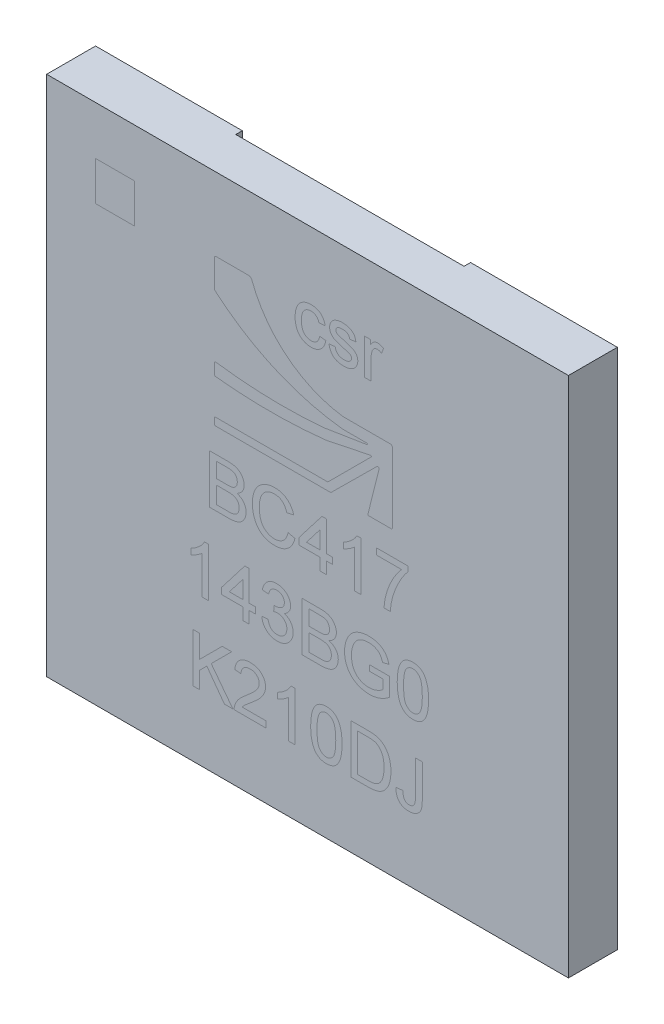
SolidWorks part; units mm, degrees
ref_plane "Спереди" through (0, 0, 0) normal (0, 0, 1) x (1, 0, 0)
ref_plane "Сверху" through (0, 0, 0) normal (0, 1, 0) x (1, 0, 0)
ref_plane "Справа" through (0, 0, 0) normal (1, 0, 0) x (0, 0, -1)
sketch "Эскиз1" plane through (0, 0, 0) normal (0, 0, 1) x (1, 0, 0)
  line L1 (4, 4) -> (-4, 4)
  line L2 (4, 4) -> (4, -4)
  line L3 (4, -4) -> (-4, -4)
  line L4 (-4, 4) -> (-4, -4)
  line L5 (4, 4) -> (-4, -4) construction
  line L6 (4, -4) -> (-4, 4) construction
  point P0 (0, 0)
  dimension "D1" = 8
  dimension "D2" = 8
extrude "Бобышка-Вытянуть1" add sketch "Эскиз1" along normal blind 0.75
sketch "Эскиз2" plane through (0, 0, 0) normal (0, 0, -1) x (-1, 0, 0)
  line L0 (0, -4) -> (0, 4) construction
  line L1 (4, -4) -> (-4, -4) construction
  line L2 (-4, 4) -> (4, 4) construction
  line L3 (4, 0) -> (-4, 0) construction
  line L4 (4, 4) -> (4, -4) construction
  line L5 (-4, -4) -> (-4, 4) construction
  line L6 (4, 4) -> (3.5986, 4) construction
  line L7 (3.5986, 4) -> (3.5986, 3.68) construction
  line L8 (3.5986, -4) -> (3.5986, -3.68) construction
  line L9 (4, -4) -> (3.5986, -4) construction
  line L10 (-4, -4) -> (-3.5986, -4) construction
  line L11 (-3.5986, -3.11) -> (-3.5986, -3.705) construction
  line L12 (-3.5986, 4) -> (-3.5986, 3.68) construction
  line L13 (-4, 4) -> (-3.5986, 4) construction
  circle A0 centre (3.5986, 3.68) radius 0.154
  circle A1 centre (3.5986, 3.11) radius 0.154
  circle A2 centre (3.5986, 2.54) radius 0.154
  circle A3 centre (3.5986, 1.97) radius 0.154
  circle A4 centre (3.5986, 1.4) radius 0.154
  circle A5 centre (3.5986, 0.83) radius 0.154
  circle A6 centre (3.5986, 0.26) radius 0.154
  circle A14 centre (3.1486, 3.11) radius 0.154
  circle A15 centre (3.1486, 2.54) radius 0.154
  circle A16 centre (3.1486, 1.97) radius 0.154
  circle A17 centre (3.1486, 1.4) radius 0.154
  circle A18 centre (3.1486, 0.83) radius 0.154
  circle A19 centre (3.1486, 0.26) radius 0.154
  circle A27 centre (2.6986, 3.11) radius 0.154
  circle A28 centre (2.6986, 2.54) radius 0.154
  circle A29 centre (2.6986, 1.97) radius 0.154
  circle A30 centre (2.6986, 1.4) radius 0.154
  circle A31 centre (2.6986, 0.83) radius 0.154
  circle A32 centre (2.6986, 0.26) radius 0.154
  circle A40 centre (2.2486, 3.11) radius 0.154
  circle A41 centre (2.2486, 2.54) radius 0.154
  circle A42 centre (2.2486, 1.97) radius 0.154
  circle A43 centre (2.2486, 1.4) radius 0.154
  circle A44 centre (2.2486, 0.83) radius 0.154
  circle A45 centre (2.2486, 0.26) radius 0.154
  circle A53 centre (3.1486, 3.68) radius 0.154
  circle A54 centre (2.6986, 3.68) radius 0.154
  circle A55 centre (2.2486, 3.68) radius 0.154
  circle A112 centre (3.5986, -0.31) radius 0.154 [skipped]
  circle A113 centre (3.5986, -0.88) radius 0.154 [skipped]
  circle A114 centre (3.5986, -1.45) radius 0.154 [skipped]
  circle A115 centre (3.5986, -2.02) radius 0.154 [skipped]
  circle A116 centre (3.5986, -2.59) radius 0.154 [skipped]
  circle A117 centre (3.5986, -3.16) radius 0.154 [skipped]
  circle A118 centre (3.5986, -3.73) radius 0.154 [skipped]
  circle A119 centre (3.1486, -0.31) radius 0.154 [skipped]
  circle A120 centre (3.1486, -0.88) radius 0.154 [skipped]
  circle A121 centre (3.1486, -1.45) radius 0.154 [skipped]
  circle A122 centre (3.1486, -2.02) radius 0.154 [skipped]
  circle A123 centre (3.1486, -2.59) radius 0.154 [skipped]
  circle A124 centre (3.1486, -3.16) radius 0.154 [skipped]
  circle A125 centre (3.1486, -3.73) radius 0.154 [skipped]
  circle A126 centre (2.6986, -0.31) radius 0.154 [skipped]
  circle A127 centre (2.6986, -0.88) radius 0.154 [skipped]
  circle A128 centre (2.6986, -1.45) radius 0.154 [skipped]
  circle A129 centre (2.6986, -2.02) radius 0.154 [skipped]
  circle A130 centre (2.6986, -2.59) radius 0.154 [skipped]
  circle A131 centre (2.6986, -3.16) radius 0.154 [skipped]
  circle A132 centre (2.6986, -3.73) radius 0.154 [skipped]
  circle A133 centre (2.2486, -0.31) radius 0.154 [skipped]
  circle A134 centre (2.2486, -0.88) radius 0.154 [skipped]
  circle A135 centre (2.2486, -1.45) radius 0.154 [skipped]
  circle A136 centre (2.2486, -2.02) radius 0.154 [skipped]
  circle A137 centre (2.2486, -2.59) radius 0.154 [skipped]
  circle A138 centre (2.2486, -3.16) radius 0.154 [skipped]
  circle A139 centre (2.2486, -3.73) radius 0.154 [skipped]
  circle A140 centre (2.2486, -3.68) radius 0.154
  circle A141 centre (2.6986, -3.68) radius 0.154
  circle A142 centre (3.1486, -3.68) radius 0.154
  circle A143 centre (2.2486, -0.26) radius 0.154
  circle A144 centre (2.2486, -0.83) radius 0.154
  circle A145 centre (2.2486, -1.4) radius 0.154
  circle A146 centre (2.2486, -1.97) radius 0.154
  circle A147 centre (2.2486, -2.54) radius 0.154
  circle A148 centre (2.2486, -3.11) radius 0.154
  circle A149 centre (2.6986, -0.26) radius 0.154
  circle A150 centre (2.6986, -0.83) radius 0.154
  circle A151 centre (2.6986, -1.4) radius 0.154
  circle A152 centre (2.6986, -1.97) radius 0.154
  circle A153 centre (2.6986, -2.54) radius 0.154
  circle A154 centre (2.6986, -3.11) radius 0.154
  circle A155 centre (3.1486, -0.26) radius 0.154
  circle A156 centre (3.1486, -0.83) radius 0.154
  circle A157 centre (3.1486, -1.4) radius 0.154
  circle A158 centre (3.1486, -1.97) radius 0.154
  circle A159 centre (3.1486, -2.54) radius 0.154
  circle A160 centre (3.1486, -3.11) radius 0.154
  circle A161 centre (3.5986, -0.26) radius 0.154
  circle A162 centre (3.5986, -0.83) radius 0.154
  circle A163 centre (3.5986, -1.4) radius 0.154
  circle A164 centre (3.5986, -1.97) radius 0.154
  circle A165 centre (3.5986, -2.54) radius 0.154
  circle A166 centre (3.5986, -3.11) radius 0.154
  circle A169 centre (-3.5986, -3.11) radius 0.154
  circle A170 centre (-3.5986, -2.54) radius 0.154
  circle A171 centre (-3.5986, -1.97) radius 0.154
  circle A172 centre (-3.5986, -1.4) radius 0.154
  circle A173 centre (-3.5986, -0.83) radius 0.154
  circle A174 centre (-3.5986, -0.26) radius 0.154
  circle A175 centre (-3.1486, -3.11) radius 0.154
  circle A176 centre (-3.1486, -2.54) radius 0.154
  circle A177 centre (-3.1486, -1.97) radius 0.154
  circle A178 centre (-3.1486, -1.4) radius 0.154
  circle A179 centre (-3.1486, -0.83) radius 0.154
  circle A180 centre (-3.1486, -0.26) radius 0.154
  circle A181 centre (-2.6986, -3.11) radius 0.154
  circle A182 centre (-2.6986, -2.54) radius 0.154
  circle A183 centre (-2.6986, -1.97) radius 0.154
  circle A184 centre (-2.6986, -1.4) radius 0.154
  circle A185 centre (-2.6986, -0.83) radius 0.154
  circle A186 centre (-2.6986, -0.26) radius 0.154
  circle A187 centre (-2.2486, -3.11) radius 0.154
  circle A188 centre (-2.2486, -2.54) radius 0.154
  circle A189 centre (-2.2486, -1.97) radius 0.154
  circle A190 centre (-2.2486, -1.4) radius 0.154
  circle A191 centre (-2.2486, -0.83) radius 0.154
  circle A192 centre (-2.2486, -0.26) radius 0.154
  circle A193 centre (-3.1486, -3.68) radius 0.154
  circle A194 centre (-2.6986, -3.68) radius 0.154
  circle A195 centre (-2.2486, -3.68) radius 0.154
  circle A196 centre (-2.2486, 3.68) radius 0.154
  circle A197 centre (-2.6986, 3.68) radius 0.154
  circle A198 centre (-3.1486, 3.68) radius 0.154
  circle A199 centre (-2.2486, 0.26) radius 0.154
  circle A200 centre (-2.2486, 0.83) radius 0.154
  circle A201 centre (-2.2486, 1.4) radius 0.154
  circle A202 centre (-2.2486, 1.97) radius 0.154
  circle A203 centre (-2.2486, 2.54) radius 0.154
  circle A204 centre (-2.2486, 3.11) radius 0.154
  circle A205 centre (-2.6986, 0.26) radius 0.154
  circle A206 centre (-2.6986, 0.83) radius 0.154
  circle A207 centre (-2.6986, 1.4) radius 0.154
  circle A208 centre (-2.6986, 1.97) radius 0.154
  circle A209 centre (-2.6986, 2.54) radius 0.154
  circle A210 centre (-2.6986, 3.11) radius 0.154
  circle A211 centre (-3.1486, 0.26) radius 0.154
  circle A212 centre (-3.1486, 0.83) radius 0.154
  circle A213 centre (-3.1486, 1.4) radius 0.154
  circle A214 centre (-3.1486, 1.97) radius 0.154
  circle A215 centre (-3.1486, 2.54) radius 0.154
  circle A216 centre (-3.1486, 3.11) radius 0.154
  circle A217 centre (-3.5986, 0.26) radius 0.154
  circle A218 centre (-3.5986, 0.83) radius 0.154
  circle A219 centre (-3.5986, 1.4) radius 0.154
  circle A220 centre (-3.5986, 1.97) radius 0.154
  circle A221 centre (-3.5986, 2.54) radius 0.154
  circle A222 centre (-3.5986, 3.11) radius 0.154
  circle A223 centre (-3.5986, 3.68) radius 0.154
  circle A224 centre (-3.5986, -3.705) radius 0.154
  dimension "D1" = 14
  dimension "D3" = 0.308
  dimension "D4" = 0.32
  dimension "D2" = 4
extrude "Бобышка-Вытянуть2" add sketch "Эскиз2" along normal blind 0.1
sketch "Эскиз3" plane through (0, 0, 0) normal (0, 0, -1) x (-1, 0, 0)
  line L9 (1.75, 3.215) -> (-1.75, 3.215)
  line L10 (1.75, 3.215) -> (1.75, -3.215)
  line L11 (1.75, -3.215) -> (-1.75, -3.215)
  line L12 (-1.75, 3.215) -> (-1.75, -3.215)
  point P0 (0, 3.215)
  dimension "D1" = 3.5
extrude "Вырез-Вытянуть2" cut sketch "Эскиз3" against normal blind 0.07
sketch "Эскиз5" plane through (0, 0, 0) normal (0, 0, -1) x (-1, 0, 0)
  line L0 (-4, 4) -> (4, 4) construction
  line L1 (-1.75, 3.215) -> (1.75, 3.215)
  line L2 (-1.75, 3.215) -> (-1.75, 4)
  line L3 (-1.75, 4) -> (1.75, 4)
  line L4 (1.75, 3.215) -> (1.75, 4)
  line L5 (4, -4) -> (-4, -4) construction
  line L6 (-1.75, -3.215) -> (1.7196, -3.215)
  line L7 (-1.75, -3.215) -> (-1.75, -4)
  line L8 (-1.75, -4) -> (1.7196, -4)
  line L9 (1.7196, -3.215) -> (1.7196, -4)
extrude "Вырез-Вытянуть3" cut sketch "Эскиз5" against normal blind 0.1
sketch "Sketch1" [suppressed] plane through (0, 0, 2) normal (0, 0, 1) x (1, 0, 0)
  line L0 (0, 0) -> (0, -0.5) construction
  line L1 (-3.4888, -0.5) -> (3.4888, -0.5) construction
  line L2 (-3.4888, -1.75) -> (3.4888, -1.75) construction
  line L3 (-3.4888, -3) -> (3.4888, -3) construction
  line L4 (-1.4092, 0.6238) -> (0.357, 0.6238)
  line L5 (0.357, 0.6238) -> (1.0627, 1.3228)
  line L6 (1.0962, 1.3038) -> (0.9219, 0.6064)
  line L7 (1.0328, 0.6064) -> (1.2808, 0.6064)
  line L8 (1.3008, 0.6264) -> (1.3008, 1.6963)
  line L9 (1.2708, 1.7263) -> (0.5438, 1.7263)
  line L10 (0.9219, 0.6064) -> (1.0328, 0.6064)
  line L11 (-1.4292, 0.6438) -> (-1.4292, 0.7212)
  line L12 (-1.4092, 0.7412) -> (0.3108, 0.7412)
  line L13 (0.3108, 0.7412) -> (0.9772, 1.4076)
  line L14 (0.9681, 1.4245) -> (0.2822, 1.2827)
  line L15 (-1.4292, 1.3008) -> (-1.4292, 1.4549)
  line L16 (-0.2926, 2.4499) -> (0.7741, 2.4499) construction
  line L17 (0.2468, 1.4313) -> (0.909, 1.5375)
  line L18 (0.9074, 1.5574) -> (0.536, 1.5574)
  line L19 (-1.4292, 2.4499) -> (-1.4292, 2.8482)
  line L20 (-1.3992, 2.8782) -> (-0.9028, 2.8782)
  line L21 (-3.2533, 3.2573) -> (-2.6533, 3.2573)
  line L22 (-3.2533, 3.2573) -> (-3.2533, 2.6573)
  line L23 (-3.2533, 2.6573) -> (-2.6533, 2.6573)
  line L24 (-2.6533, 3.2573) -> (-2.6533, 2.6573)
  line L25 (-3.2533, 3.2573) -> (-2.6533, 2.6573) construction
  line L26 (-3.2533, 2.6573) -> (-2.6533, 3.2573) construction
  arc A0 (0.2822, 1.2827) -> (-1.4114, 1.2809) centre (-0.5729, 9.0729) cw
  arc A1 (-1.4064, 1.4747) -> (0.2468, 1.4313) centre (-0.3872, 8.7808) ccw
  arc A2 (-1.4119, 2.412) -> (0.536, 1.5574) centre (0.947, 5.1414) ccw
  arc A3 (0.5438, 1.7263) -> (-0.8559, 2.8456) centre (0.7741, 3.449) cw
  arc A4 (1.2808, 0.6064) -> (1.3008, 0.6264) centre (1.2808, 0.6264) ccw
  arc A5 (1.0627, 1.3228) -> (1.0962, 1.3038) centre (1.0768, 1.3086) cw
  arc A6 (-1.4292, 1.3008) -> (-1.4114, 1.2809) centre (-1.4092, 1.3008) ccw
  arc A7 (-1.4292, 1.4549) -> (-1.4064, 1.4747) centre (-1.4092, 1.4549) cw
  arc A8 (-1.4292, 0.7212) -> (-1.4092, 0.7412) centre (-1.4092, 0.7212) cw
  arc A9 (-1.4092, 0.6238) -> (-1.4292, 0.6438) centre (-1.4092, 0.6438) cw
  arc A10 (0.9772, 1.4076) -> (0.9681, 1.4245) centre (0.9701, 1.4147) ccw
  arc A11 (0.909, 1.5375) -> (0.9074, 1.5574) centre (0.9074, 1.5474) ccw
  arc A12 (1.3008, 1.6963) -> (1.2708, 1.7263) centre (1.2708, 1.6963) ccw
  arc A13 (-1.4292, 2.4499) -> (-1.4119, 2.412) centre (-1.3792, 2.4499) ccw
  arc A14 (-0.9028, 2.8782) -> (-0.8559, 2.8456) centre (-0.9028, 2.8282) cw
  arc A15 (-1.4292, 2.8482) -> (-1.3992, 2.8782) centre (-1.3992, 2.8482) cw
  text T0 "BC417" font "Arial" height 0.75
  text T1 "143BG0" font "Arial" height 0.75
  text T2 "K210DJ" font "Arial" height 0.75
  text T3 "csr" font "Arial" height 0.75
  point P6 (0, -0.5)
  point P10 (0, -1.75)
  point P12 (0, -3)
  point P49 (-1.4292, 1.4779)
  point P52 (-1.4292, 0.7412)
  point P72 (-2.9533, 2.9573)
  dimension "D4" = 0.02
  dimension "D5" = 0.01
  dimension "D6" = 0.03
  dimension "D7" = 0.05
  dimension "D8" = 0.03
  dimension "D1" = 0.5
  dimension "D2" = 1.25
  dimension "D3" = 1.25
  dimension "D9" = 0.6
sketch "Sketch2" plane through (0, 0, 0.75) normal (0, 0, 1) x (1, 0, 0)
  line L0 (0, 0) -> (0, -0.5) construction
  line L1 (-3.0209, -0.5) -> (3.0209, -0.5) construction
  line L2 (-3.0209, -1.75) -> (3.0209, -1.75) construction
  line L3 (-3.0209, -3) -> (3.0209, -3) construction
  line L4 (-2.6533, 3.2573) -> (-3.2533, 3.2573)
  line L5 (-2.6533, 2.6573) -> (-2.6533, 3.2573)
  line L6 (-3.2533, 2.6573) -> (-2.6533, 2.6573)
  line L7 (-3.2533, 3.2573) -> (-3.2533, 2.6573)
  line L8 (-2.6533, 3.2573) -> (-3.2533, 3.2573)
  line L9 (-2.6533, 2.6573) -> (-2.6533, 3.2573)
  line L10 (-3.2533, 2.6573) -> (-2.6533, 2.6573)
  line L11 (-3.2533, 3.2573) -> (-3.2533, 2.6573)
  line L12 (-0.2292, 2.412) -> (1.7636, 2.412) construction
  line L24 (-1.4292, 2.8482) -> (-1.4292, 2.4499)
  line L25 (0.536, 1.5574) -> (0.9074, 1.5574)
  line L26 (0.909, 1.5375) -> (0.2468, 1.4313)
  line L27 (-1.4292, 1.4549) -> (-1.4292, 1.3008)
  line L28 (0.2822, 1.2827) -> (0.9681, 1.4245)
  line L29 (0.9772, 1.4076) -> (0.3108, 0.7412)
  line L30 (0.3108, 0.7412) -> (-1.4092, 0.7412)
  line L31 (-1.4292, 0.7212) -> (-1.4292, 0.6438)
  line L32 (-1.4092, 0.6238) -> (0.357, 0.6238)
  line L33 (0.357, 0.6238) -> (1.0627, 1.3228)
  line L34 (1.0962, 1.3038) -> (0.9219, 0.6064)
  line L35 (0.9219, 0.6064) -> (1.0328, 0.6064)
  line L36 (1.0328, 0.6064) -> (1.2808, 0.6064)
  line L37 (1.3008, 0.6264) -> (1.3008, 1.6963)
  line L38 (1.2708, 1.7263) -> (0.5438, 1.7263)
  line L39 (-0.9028, 2.8782) -> (-1.3992, 2.8782)
  line L40 (-1.4292, 2.8482) -> (-1.4292, 2.4499)
  line L41 (0.536, 1.5574) -> (0.9074, 1.5574)
  line L42 (0.909, 1.5375) -> (0.2468, 1.4313)
  line L43 (-1.4292, 1.4549) -> (-1.4292, 1.3008)
  line L44 (0.2822, 1.2827) -> (0.9681, 1.4245)
  line L45 (0.9772, 1.4076) -> (0.3108, 0.7412)
  line L46 (0.3108, 0.7412) -> (-1.4092, 0.7412)
  line L47 (-1.4292, 0.7212) -> (-1.4292, 0.6438)
  line L48 (-1.4092, 0.6238) -> (0.357, 0.6238)
  line L49 (0.357, 0.6238) -> (1.0627, 1.3228)
  line L50 (1.0962, 1.3038) -> (0.9219, 0.6064)
  line L51 (0.9219, 0.6064) -> (1.0328, 0.6064)
  line L52 (1.0328, 0.6064) -> (1.2808, 0.6064)
  line L53 (1.3008, 0.6264) -> (1.3008, 1.6963)
  line L54 (1.2708, 1.7263) -> (0.5438, 1.7263)
  line L55 (-0.9028, 2.8782) -> (-1.3992, 2.8782)
  arc A16 (-1.4292, 2.4499) -> (-1.4119, 2.412) centre (-1.3792, 2.4499) ccw
  arc A17 (-1.4119, 2.412) -> (0.536, 1.5574) centre (0.947, 5.1414) ccw
  arc A18 (0.909, 1.5375) -> (0.9074, 1.5574) centre (0.9074, 1.5474) ccw
  arc A19 (-1.4064, 1.4747) -> (0.2468, 1.4313) centre (-0.3872, 8.7808) ccw
  arc A20 (-1.4064, 1.4747) -> (-1.4292, 1.4549) centre (-1.4092, 1.4549) ccw
  arc A21 (-1.4292, 1.3008) -> (-1.4114, 1.2809) centre (-1.4092, 1.3008) ccw
  arc A22 (-1.4114, 1.2809) -> (0.2822, 1.2827) centre (-0.5729, 9.0729) ccw
  arc A23 (0.9772, 1.4076) -> (0.9681, 1.4245) centre (0.9701, 1.4147) ccw
  arc A24 (-1.4092, 0.7412) -> (-1.4292, 0.7212) centre (-1.4092, 0.7212) ccw
  arc A25 (-1.4292, 0.6438) -> (-1.4092, 0.6238) centre (-1.4092, 0.6438) ccw
  arc A26 (1.0962, 1.3038) -> (1.0627, 1.3228) centre (1.0768, 1.3086) ccw
  arc A27 (1.2808, 0.6064) -> (1.3008, 0.6264) centre (1.2808, 0.6264) ccw
  arc A28 (1.3008, 1.6963) -> (1.2708, 1.7263) centre (1.2708, 1.6963) ccw
  arc A29 (-0.8559, 2.8456) -> (0.5438, 1.7263) centre (0.7741, 3.449) ccw
  arc A30 (-0.8559, 2.8456) -> (-0.9028, 2.8782) centre (-0.9028, 2.8282) ccw
  arc A31 (-1.3992, 2.8782) -> (-1.4292, 2.8482) centre (-1.3992, 2.8482) ccw
  arc A32 (-1.4292, 2.4499) -> (-1.4119, 2.412) centre (-1.3792, 2.4499) ccw
  arc A33 (-1.4119, 2.412) -> (0.536, 1.5574) centre (0.947, 5.1414) ccw
  arc A34 (0.909, 1.5375) -> (0.9074, 1.5574) centre (0.9074, 1.5474) ccw
  arc A35 (-1.4064, 1.4747) -> (0.2468, 1.4313) centre (-0.3872, 8.7808) ccw
  arc A36 (-1.4064, 1.4747) -> (-1.4292, 1.4549) centre (-1.4092, 1.4549) ccw
  arc A37 (-1.4292, 1.3008) -> (-1.4114, 1.2809) centre (-1.4092, 1.3008) ccw
  arc A38 (-1.4114, 1.2809) -> (0.2822, 1.2827) centre (-0.5729, 9.0729) ccw
  arc A39 (0.9772, 1.4076) -> (0.9681, 1.4245) centre (0.9701, 1.4147) ccw
  arc A40 (-1.4092, 0.7412) -> (-1.4292, 0.7212) centre (-1.4092, 0.7212) ccw
  arc A41 (-1.4292, 0.6438) -> (-1.4092, 0.6238) centre (-1.4092, 0.6438) ccw
  arc A42 (1.0962, 1.3038) -> (1.0627, 1.3228) centre (1.0768, 1.3086) ccw
  arc A43 (1.2808, 0.6064) -> (1.3008, 0.6264) centre (1.2808, 0.6264) ccw
  arc A44 (1.3008, 1.6963) -> (1.2708, 1.7263) centre (1.2708, 1.6963) ccw
  arc A45 (-0.8559, 2.8456) -> (0.5438, 1.7263) centre (0.7741, 3.449) ccw
  arc A46 (-0.8559, 2.8456) -> (-0.9028, 2.8782) centre (-0.9028, 2.8282) ccw
  arc A47 (-1.3992, 2.8782) -> (-1.4292, 2.8482) centre (-1.3992, 2.8482) ccw
  text T0 "BC417" font "Arial" height 0.75
  text T1 "143BG0\r\n" font "Arial" height 0.75
  text T2 "K210DJ" font "Arial" height 0.75
  text T3 "csr" font "Arial" height 0.75
  point P22 (0, -0.5)
  dimension "D3" = 0.5
  dimension "D1" = 0
  dimension "D2" = 0
  dimension "D4" = 1.25
  dimension "D5" = 1.25
split line "Split Line1"
